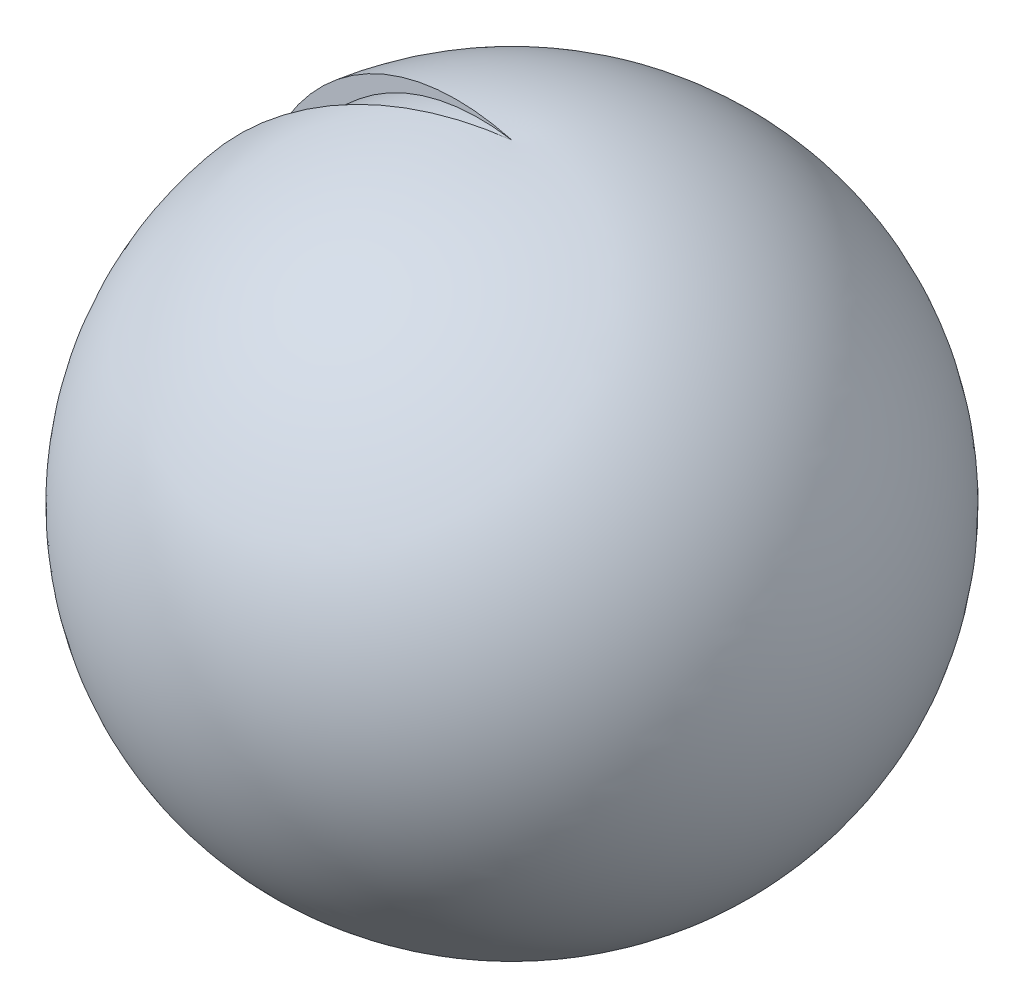
SolidWorks part; units mm, degrees
ref_plane "Front Plane" through (0, 0, 0) normal (0, 0, 1) x (1, 0, 0)
ref_plane "Top Plane" through (0, 0, 0) normal (0, 1, 0) x (1, 0, 0)
ref_plane "Right Plane" through (0, 0, 0) normal (1, 0, 0) x (0, 0, -1)
sketch "Model" plane through (0, 0, 0) normal (0, 0, 1) x (1, 0, 0)
  line L0 (-57.451, 0.2514) -> (0, 0) construction
  line L1 (0, 0) -> (0, -40.0437) construction
  line L2 (140.5442, 151.5034) -> (140.5442, -461.6138)
  line L3 (0, 756.2324) -> (0, 1202.6699)
  arc A0 (548.6559, -409.6807) -> (0, 1202.6699) centre (40.0019, 316.7574) ccw
  arc A2 (140.5442, -461.6138) -> (548.6559, -409.6807) centre (295.2415, -47.7675) ccw
  arc A3 (140.5442, 151.5034) -> (78.5049, 506.3195) centre (40, 316.7551) ccw
  arc A5 (78.5049, 506.3195) -> (0, 756.2324) centre (-363.307, 504.8203) ccw
sketch "Sketch2" plane through (0, 0, 0) normal (0, 0, 1) x (1, 0, 0)
  line L0 (-57.451, 0.2514) -> (0, 0) construction
  line L1 (0, 0) -> (0, -40.0437) construction
  line L3 (0, 756.2324) -> (0, 1202.6699)
  arc A0 (0, 1202.6699) -> (-763.728, 691.5366) centre (40.0019, 316.7574) ccw
  arc A1 (-763.728, 691.5366) -> (-438.5503, 69.4602) centre (-363.307, 504.8203) ccw
  arc A4 (-78.1672, 842.3041) -> (-438.5503, 69.4602) centre (40, 316.7551) ccw
  arc A5 (0, 756.2324) -> (-78.1672, 842.3041) centre (-363.307, 504.8203) ccw
revolve "Revolve1" add sketch "Model" angle 340 mid plane about L3
revolve "Revolve2" add sketch "Sketch2" angle 20 mid plane about L3
